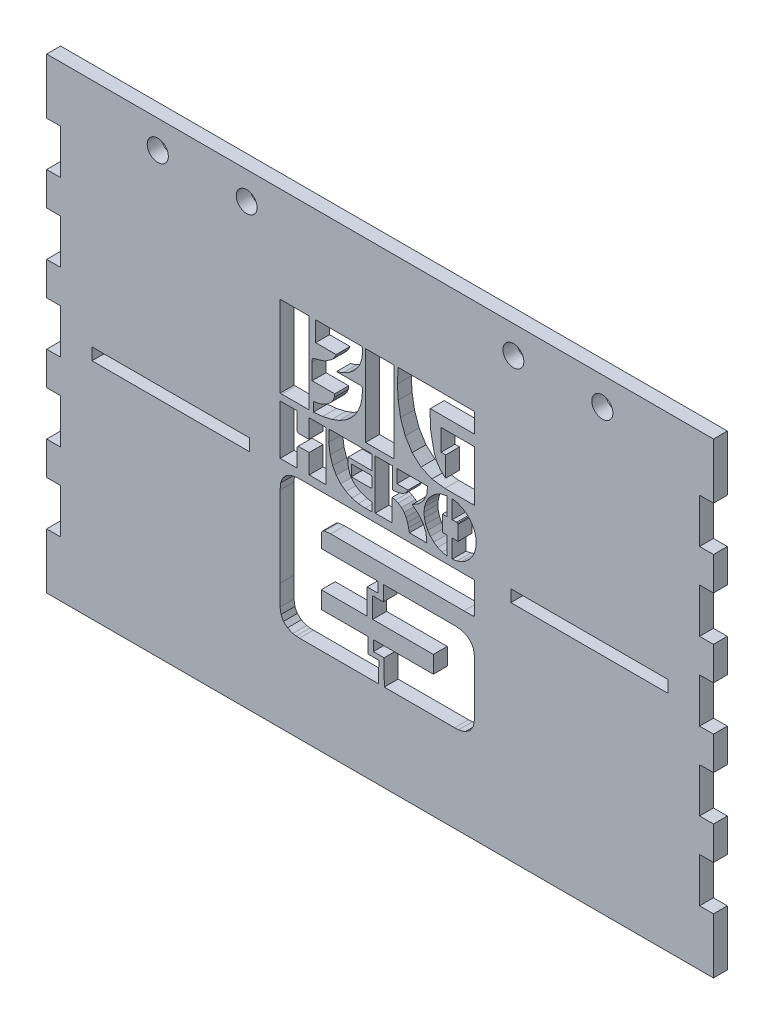
SolidWorks part; units mm, degrees
ref_plane "Front Plane" through (0, 0, 0) normal (0, 0, 1) x (1, 0, 0)
ref_plane "Top Plane" through (0, 0, 0) normal (0, 1, 0) x (1, 0, 0)
ref_plane "Right Plane" through (0, 0, 0) normal (1, 0, 0) x (0, 0, -1)
sketch "Sketch1" plane through (0, 0, 0) normal (0, 0, 1) x (1, 0, 0)
  line L0 (-83.4402, 53.069) -> (-83.4402, 40.369) construction
  line L1 (-83.4402, 53.069) -> (68.9598, 53.069)
  line L2 (-83.4402, 53.069) -> (-83.4402, -53.611)
  line L3 (-83.4402, -53.611) -> (68.9598, -53.611)
  line L4 (68.9598, 53.069) -> (68.9598, -53.611)
  line L5 (-83.4402, 46.719) -> (-58.0402, 46.719) construction
  line L6 (-7.2402, 53.069) -> (-7.2402, -53.611) construction
  line L7 (-47.8802, 46.719) -> (-37.7202, 46.719) construction
  line L8 (-55.6272, 46.719) -> (-47.8802, 46.719) construction
  line L9 (41.1468, 46.719) -> (33.3998, 46.719) construction
  line L10 (33.3998, 46.719) -> (23.2398, 46.719) construction
  line L11 (68.9598, 46.719) -> (43.5598, 46.719) construction
  line L12 (68.9598, -0.271) -> (-83.4402, -0.271) construction
  circle A0 centre (-58.0402, 46.719) radius 2.413
  circle A2 centre (-37.7202, 46.719) radius 2.3847
  circle A3 centre (23.2398, 46.719) radius 2.3847
  circle A5 centre (43.5598, 46.719) radius 2.413
  dimension "D4" = 4.826
  dimension "D7" = 10.16
  dimension "D8" = 4.7693
  dimension "D1" = 106.68
  dimension "D2" = 152.4
  dimension "D3" = 12.7
  dimension "D5" = 25.4
  dimension "D6" = 7.747
extrude "Boss-Extrude1" add sketch "Sketch1" along normal blind 3.175
sketch "Sketch2" plane through (0, 0, 3.175) normal (0, 0, 1) x (1, 0, 0)
  line L0 (-83.4402, 53.069) -> (-83.4402, -53.611) construction
  line L1 (-83.4402, 40.369) -> (-80.2652, 40.369)
  line L2 (-83.4402, 40.369) -> (-83.4402, 30.209)
  line L3 (-83.4402, 30.209) -> (-80.2652, 30.209)
  line L4 (-80.2652, 40.369) -> (-80.2652, 30.209)
  line L5 (-83.4402, 40.369) -> (-83.4402, 53.069) construction
  line L6 (-83.4402, 30.209) -> (-83.4402, -53.611) construction
  dimension "D1" = 3.175
  dimension "D2" = 12.7
  dimension "D3" = 10.16
extrude "Cut-Extrude1" cut sketch "Sketch2" against normal through all contours L4 L3 L2 L1
pattern_linear "LPattern1" count 5 spacing 17.78 along (0, -1, 0) of "Cut-Extrude1"
ref_plane "Plane1" through (-7.2402, 0, 0) normal (-1, 0, 0) x (0, 0, 1)
mirror "Mirror1" about plane through (-7.2402, 0, 0) normal (-1, 0, 0) of "LPattern1", "Cut-Extrude1"
sketch "Sketch3" plane through (0, 0.4582, 0) normal (0, 0, -1) x (-1, 0, 0)
  line L0 (22.4861, 14.3643) -> (22.4861, 12.2032)
  line L54 (7.2402, 52.6108) -> (7.2402, -54.0692) construction
  line L99 (-58.5963, -0.1731) -> (-22.6521, -0.1731)
  line L256 (-58.5963, -0.1731) -> (-58.5963, -2.9203)
  line L275 (-58.5963, -2.9203) -> (-22.6521, -2.9203)
  line L276 (-22.6521, -0.1731) -> (-22.6521, -2.9203)
  line L278 (-68.9598, 52.6108) -> (83.4402, 52.6108) construction
  line L280 (83.4402, -54.0692) -> (-68.9598, -54.0692) construction
  line L281 (37.1325, -0.1731) -> (37.1325, -2.9203)
  line L282 (73.0766, -2.9203) -> (37.1325, -2.9203)
  line L283 (73.0766, -0.1731) -> (73.0766, -2.9203)
  line L284 (73.0766, -0.1731) -> (37.1325, -0.1731)
  line L285 (21.9553, 26.2147) -> (21.9559, 30.7644)
  line L286 (10.1811, -16.2374) -> (10.2041, -22.0279)
  line L287 (7.7211, -16.2367) -> (10.1811, -16.2374)
  line L288 (7.7081, -13.8815) -> (7.7211, -16.2367)
  line L289 (8.9509, -17.3486) -> (8.918, -22.0279)
  line L290 (6.4902, -17.3486) -> (8.9509, -17.3486)
  line L291 (6.5045, -13.8809) -> (6.4902, -17.3486)
  line L292 (6.2986, -28.3222) -> (6.2763, -34.1128)
  line L293 (8.7592, -28.3222) -> (6.2986, -28.3222)
  line L294 (8.7592, -25.9557) -> (8.7592, -28.3222)
  line L295 (7.5289, -29.4334) -> (7.5624, -34.1128)
  line L296 (9.9895, -29.4334) -> (7.5289, -29.4334)
  line L297 (9.9945, -25.9557) -> (9.9895, -29.4334)
  line L298 (3.3859, 7.5801) -> (3.3989, 10.6193)
  line L299 (4.4518, 7.5801) -> (4.4476, 10.6193)
  line L300 (-9.2452, -1.0277) -> (-9.2452, 3.1617)
  line L301 (-8.054, -1.0016) -> (-8.0547, 3.1617)
  line L302 (-9.2452, 6.7777) -> (-9.2452, 10.9337)
  line L303 (-8.0547, 6.7759) -> (-8.0547, 10.9145)
  line L304 (13.8169, 3.7404) -> (13.8169, 6.3195)
  line L305 (9.3025, 3.7521) -> (13.8169, 3.7404)
  line L306 (9.1437, 3.852) -> (9.3025, 3.7521)
  line L307 (9.0494, 4.0225) -> (9.1437, 3.852)
  line L308 (9.0501, 6.0188) -> (9.0494, 4.0225)
  line L309 (9.1535, 6.201) -> (9.0501, 6.0188)
  line L310 (9.3266, 6.3065) -> (9.1535, 6.201)
  line L311 (13.8169, 6.3195) -> (9.3266, 6.3065)
  line L312 (9.0686, 7.3141) -> (14.5095, 7.3141)
  line L313 (9.0686, 10.6132) -> (9.0686, 7.3141)
  line L314 (9.267, 10.6558) -> (9.0686, 10.6132)
  line L315 (18.5775, 10.6634) -> (9.267, 10.6558)
  line L316 (18.8422, 10.5784) -> (18.5775, 10.6634)
  line L317 (18.9278, 10.3129) -> (18.8422, 10.5784)
  line L318 (18.9681, 7.9775) -> (18.9278, 10.3129)
  line L319 (18.6464, 5.6652) -> (18.9681, 7.9775)
  line L320 (18.0709, 3.8334) -> (18.6464, 5.6652)
  line L321 (17.2524, 2.3327) -> (18.0709, 3.8334)
  line L322 (16.2235, 1.1451) -> (17.2524, 2.3327)
  line L323 (15.0179, 0.2498) -> (16.2235, 1.1451)
  line L324 (13.6675, -0.3722) -> (15.0179, 0.2498)
  line L325 (12.2058, -0.74) -> (13.6675, -0.3722)
  line L326 (10.6642, -0.8739) -> (12.2058, -0.74)
  line L327 (9.0761, -0.7927) -> (10.6642, -0.8739)
  line L328 (9.0761, 1.0696) -> (9.0761, -0.7927)
  line L329 (10.4733, 1.3585) -> (9.0761, 1.0696)
  line L330 (11.6743, 1.7982) -> (10.4733, 1.3585)
  line L331 (12.6759, 2.3829) -> (11.6743, 1.7982)
  line L332 (13.472, 3.1079) -> (12.6759, 2.3829)
  line L333 (14.0586, 3.9685) -> (13.472, 3.1079)
  line L334 (14.4301, 4.9596) -> (14.0586, 3.9685)
  line L335 (14.582, 6.0771) -> (14.4301, 4.9596)
  line L336 (14.5095, 7.3141) -> (14.582, 6.0771)
  line L337 (26.2049, -0.1731) -> (26.2049, -0.7245)
  line L338 (26.195, 3.3237) -> (26.2049, -0.1731)
  line L339 (26.1163, 3.5692) -> (26.195, 3.3237)
  line L340 (25.9798, 3.7144) -> (26.1163, 3.5692)
  line L341 (23.4466, 3.7316) -> (25.9798, 3.7144)
  line L342 (23.4466, -0.7108) -> (23.4466, 3.7316)
  line L343 (19.5902, -0.7108) -> (23.4466, -0.7108)
  line L344 (19.5902, 10.628) -> (19.5902, -0.7108)
  line L345 (23.472, 10.628) -> (19.5902, 10.628)
  line L346 (23.472, 6.322) -> (23.472, 10.628)
  line L347 (25.7572, 6.3145) -> (23.472, 6.322)
  line L348 (25.9867, 6.3356) -> (25.7572, 6.3145)
  line L349 (26.1262, 6.42) -> (25.9867, 6.3356)
  line L350 (26.195, 6.5706) -> (26.1262, 6.42)
  line L351 (26.2111, 6.7908) -> (26.195, 6.5706)
  line L352 (26.2062, 10.1066) -> (26.2111, 6.7908)
  line L353 (26.2409, 10.6329) -> (26.2062, 10.1066)
  line L354 (30.0627, 10.6329) -> (26.2409, 10.6329)
  line L355 (30.0627, -0.7245) -> (30.0627, 10.6329)
  line L356 (26.2049, -0.7245) -> (30.0627, -0.7245)
  line L357 (-6.9992, 10.6883) -> (-8.0547, 10.9145)
  line L358 (-6.0194, 10.2788) -> (-6.9992, 10.6883)
  line L359 (-5.1333, 9.7053) -> (-6.0194, 10.2788)
  line L360 (-4.3613, 8.9878) -> (-5.1333, 9.7053)
  line L361 (-3.7225, 8.1444) -> (-4.3613, 8.9878)
  line L362 (-3.237, 7.1951) -> (-3.7225, 8.1444)
  line L363 (-2.9232, 6.1588) -> (-3.237, 7.1951)
  line L364 (-2.8022, 5.0543) -> (-2.9232, 6.1588)
  line L365 (-2.8904, 3.9184) -> (-2.8022, 5.0543)
  line L366 (-3.1792, 2.8506) -> (-2.8904, 3.9184)
  line L367 (-3.6506, 1.8708) -> (-3.1792, 2.8506)
  line L368 (-4.2842, 0.9994) -> (-3.6506, 1.8708)
  line L369 (-5.0608, 0.2566) -> (-4.2842, 0.9994)
  line L370 (-5.9611, -0.338) -> (-5.0608, 0.2566)
  line L371 (-6.9652, -0.7641) -> (-5.9611, -0.338)
  line L372 (-8.054, -1.0016) -> (-6.9652, -0.7641)
  line L373 (-10.3564, -0.8355) -> (-9.2452, -1.0277)
  line L374 (-11.3859, -0.4492) -> (-10.3564, -0.8355)
  line L375 (-12.3137, 0.1127) -> (-11.3859, -0.4492)
  line L376 (-13.1204, 0.8308) -> (-12.3137, 0.1127)
  line L377 (-13.7858, 1.6847) -> (-13.1204, 0.8308)
  line L378 (-14.29, 2.6558) -> (-13.7858, 1.6847)
  line L379 (-14.6137, 3.7249) -> (-14.29, 2.6558)
  line L380 (-14.7364, 4.8714) -> (-14.6137, 3.7249)
  line L381 (-14.6417, 6.0404) -> (-14.7364, 4.8714)
  line L382 (-14.3377, 7.1324) -> (-14.6417, 6.0404)
  line L383 (-13.8448, 8.1277) -> (-14.3377, 7.1324)
  line L384 (-13.1831, 9.0058) -> (-13.8448, 8.1277)
  line L385 (-12.372, 9.7456) -> (-13.1831, 9.0058)
  line L386 (-11.4325, 10.3279) -> (-12.372, 9.7456)
  line L387 (-10.3832, 10.7303) -> (-11.4325, 10.3279)
  line L388 (-9.2452, 10.9337) -> (-10.3832, 10.7303)
  line L389 (-10.2368, 6.7647) -> (-9.2452, 6.7777)
  line L390 (-10.4452, 6.6802) -> (-10.2368, 6.7647)
  line L391 (-10.5669, 6.5364) -> (-10.4452, 6.6802)
  line L392 (-10.5822, 3.1617) -> (-10.5669, 6.5364)
  line L393 (-9.2452, 3.1617) -> (-10.5822, 3.1617)
  line L394 (-6.9999, 3.1617) -> (-8.0547, 3.1617)
  line L395 (-6.9999, 6.7759) -> (-6.9999, 3.1617)
  line L396 (-7.8822, 6.7759) -> (-6.9999, 6.7759)
  line L397 (-8.0547, 6.7759) -> (-7.8822, 6.7759)
  line L398 (8.3443, 10.6193) -> (4.4476, 10.6193)
  line L399 (8.3443, -0.7134) -> (8.3443, 10.6193)
  line L400 (4.4655, -0.7134) -> (8.3443, -0.7134)
  line L401 (4.4655, 4.3581) -> (4.4655, -0.7134)
  line L402 (3.748, 4.1467) -> (4.4655, 4.3581)
  line L403 (3.1123, 3.9147) -> (3.748, 4.1467)
  line L404 (2.331, 3.4104) -> (3.1123, 3.9147)
  line L405 (1.7301, 2.7593) -> (2.331, 3.4104)
  line L406 (1.2806, 1.9905) -> (1.7301, 2.7593)
  line L407 (0.9532, 1.1315) -> (1.2806, 1.9905)
  line L408 (0.7262, 0.2151) -> (0.9532, 1.1315)
  line L409 (0.5333, -0.717) -> (0.7262, 0.2151)
  line L410 (-3.4404, -0.717) -> (0.5333, -0.717)
  line L411 (-3.2643, 1.1434) -> (-3.4404, -0.717)
  line L412 (-2.6069, 2.7258) -> (-3.2643, 1.1434)
  line L413 (-1.5304, 4.0716) -> (-2.6069, 2.7258)
  line L414 (-0.0998, 5.2199) -> (-1.5304, 4.0716)
  line L415 (-1.6433, 6.1446) -> (-0.0998, 5.2199)
  line L416 (-2.7644, 7.3817) -> (-1.6433, 6.1446)
  line L417 (-3.4348, 8.8874) -> (-2.7644, 7.3817)
  line L418 (-3.6284, 10.6193) -> (-3.4348, 8.8874)
  line L419 (3.3989, 10.6193) -> (-3.6284, 10.6193)
  line L420 (0.8836, 7.5801) -> (3.3859, 7.5801)
  line L421 (1.2508, 6.8454) -> (0.8836, 7.5801)
  line L422 (2.0929, 6.2934) -> (1.2508, 6.8454)
  line L423 (3.2229, 5.9529) -> (2.0929, 6.2934)
  line L424 (4.4518, 5.8513) -> (3.2229, 5.9529)
  line L425 (4.4518, 7.5801) -> (4.4518, 5.8513)
  line L426 (10.5433, 12.1783) -> (10.5433, 30.7533)
  line L427 (4.037, 12.1783) -> (10.5433, 12.1783)
  line L428 (4.037, 30.7533) -> (4.037, 12.1783)
  line L429 (10.5433, 30.7533) -> (4.037, 30.7533)
  line L430 (-6.7077, 23.7794) -> (-14.3197, 23.7794)
  line L431 (-6.7077, 18.8638) -> (-6.7077, 23.7794)
  line L432 (-7.7595, 18.8638) -> (-6.7077, 18.8638)
  line L433 (-7.7595, 14.2544) -> (-7.7595, 18.8638)
  line L434 (-7.1368, 14.7456) -> (-7.7595, 14.2544)
  line L435 (-6.6167, 15.2088) -> (-7.1368, 14.7456)
  line L436 (-5.6952, 16.5539) -> (-6.6167, 15.2088)
  line L437 (-5.1054, 18.0738) -> (-5.6952, 16.5539)
  line L438 (-4.3259, 22.0295) -> (-5.1054, 18.0738)
  line L439 (-4.1658, 26.059) -> (-4.3259, 22.0295)
  line L440 (-4.2377, 26.2674) -> (-4.1658, 26.059)
  line L441 (-14.3128, 26.2674) -> (-4.2377, 26.2674)
  line L442 (-14.3128, 30.7595) -> (-14.3128, 26.2674)
  line L443 (3.0826, 30.7595) -> (-14.3128, 30.7595)
  line L444 (3.123, 30.504) -> (3.0826, 30.7595)
  line L445 (3.2736, 27.3762) -> (3.123, 30.504)
  line L446 (3.0938, 24.2513) -> (3.2736, 27.3762)
  line L447 (2.5518, 21.0603) -> (3.0938, 24.2513)
  line L448 (1.4884, 18.0012) -> (2.5518, 21.0603)
  line L449 (-0.0856, 15.4661) -> (1.4884, 18.0012)
  line L450 (-2.117, 13.6388) -> (-0.0856, 15.4661)
  line L451 (-4.6131, 12.5318) -> (-2.117, 13.6388)
  line L452 (-7.5803, 12.156) -> (-4.6131, 12.5318)
  line L453 (-13.8008, 12.1517) -> (-7.5803, 12.156)
  line L454 (-14.3197, 12.1517) -> (-13.8008, 12.1517)
  line L455 (-14.3197, 23.7794) -> (-14.3197, 12.1517)
  line L456 (30.0546, 30.7644) -> (23.4981, 30.7644)
  line L457 (30.0546, 12.1857) -> (30.0546, 30.7644)
  line L458 (29.6968, 12.1665) -> (30.0546, 12.1857)
  line L459 (23.4981, 12.1727) -> (29.6968, 12.1665)
  line L460 (20.3448, 12.4252) -> (22.4861, 12.2032)
  line L461 (18.2378, 12.8988) -> (20.3448, 12.4252)
  line L462 (16.6235, 13.5017) -> (18.2378, 12.8988)
  line L463 (15.204, 14.2936) -> (16.6235, 13.5017)
  line L464 (13.9887, 15.2635) -> (15.204, 14.2936)
  line L465 (12.9853, 16.3988) -> (13.9887, 15.2635)
  line L466 (12.2033, 17.688) -> (12.9853, 16.3988)
  line L467 (11.6507, 19.1187) -> (12.2033, 17.688)
  line L468 (11.337, 20.6789) -> (11.6507, 19.1187)
  line L469 (11.2694, 22.3568) -> (11.337, 20.6789)
  line L470 (11.3023, 22.6124) -> (11.2694, 22.3568)
  line L471 (11.3922, 22.78) -> (11.3023, 22.6124)
  line L472 (11.559, 22.8716) -> (11.3922, 22.78)
  line L473 (11.822, 22.8959) -> (11.559, 22.8716)
  line L474 (16.7251, 22.8865) -> (11.822, 22.8959)
  line L475 (17.1867, 22.8865) -> (16.7251, 22.8865)
  line L476 (15.756, 23.3678) -> (17.1867, 22.8865)
  line L477 (14.4952, 24.0295) -> (15.756, 23.3678)
  line L478 (13.4188, 24.8535) -> (14.4952, 24.0295)
  line L479 (12.542, 25.8216) -> (13.4188, 24.8535)
  line L480 (11.8783, 26.9153) -> (12.542, 25.8216)
  line L481 (11.4437, 28.1159) -> (11.8783, 26.9153)
  line L482 (11.2527, 29.4052) -> (11.4437, 28.1159)
  line L483 (11.3198, 30.7644) -> (11.2527, 29.4052)
  line L484 (21.9559, 30.7644) -> (11.3198, 30.7644)
  line L485 (17.2771, 26.2147) -> (21.9553, 26.2147)
  line L486 (17.6431, 25.4253) -> (17.2771, 26.2147)
  line L487 (18.1861, 24.768) -> (17.6431, 25.4253)
  line L488 (19.9343, 23.6027) -> (18.1861, 24.768)
  line L489 (21.946, 22.9976) -> (19.9343, 23.6027)
  line L490 (22.4173, 22.8928) -> (21.946, 22.9976)
  line L491 (22.6604, 22.7569) -> (22.4173, 22.8928)
  line L492 (22.7502, 22.4927) -> (22.6604, 22.7569)
  line L493 (22.7632, 22.0016) -> (22.7502, 22.4927)
  line L494 (22.7632, 18.2822) -> (22.7632, 22.0016)
  line L495 (17.5933, 18.2822) -> (22.7632, 18.2822)
  line L496 (17.6665, 17.548) -> (17.5933, 18.2822)
  line L497 (17.9518, 16.8484) -> (17.6665, 17.548)
  line L498 (18.4206, 16.2016) -> (17.9518, 16.8484)
  line L499 (19.0432, 15.6249) -> (18.4206, 16.2016)
  line L500 (19.7904, 15.1356) -> (19.0432, 15.6249)
  line L501 (20.6332, 14.7505) -> (19.7904, 15.1356)
  line L502 (21.5416, 14.4883) -> (20.6332, 14.7505)
  line L503 (22.4861, 14.3643) -> (21.5416, 14.4883)
  line L504 (20.1302, -13.8845) -> (7.7081, -13.8815)
  line L505 (20.6326, -13.8845) -> (20.1302, -13.8845)
  line L506 (20.6276, -10.8702) -> (20.6326, -13.8845)
  line L507 (20.5687, -10.549) -> (20.6276, -10.8702)
  line L508 (20.413, -10.3009) -> (20.5687, -10.549)
  line L509 (20.1768, -10.1272) -> (20.413, -10.3009)
  line L510 (19.8742, -10.0293) -> (20.1768, -10.1272)
  line L511 (18.5229, -9.9114) -> (19.8742, -10.0293)
  line L512 (-11.9558, -9.9072) -> (18.5229, -9.9114)
  line L513 (-13.9091, -9.914) -> (-11.9558, -9.9072)
  line L514 (-14.1206, -9.8984) -> (-13.9091, -9.914)
  line L515 (-14.2572, -9.8285) -> (-14.1206, -9.8984)
  line L516 (-14.329, -9.6913) -> (-14.2572, -9.8285)
  line L517 (-14.3482, -9.4781) -> (-14.329, -9.6913)
  line L518 (-14.3414, -6.0264) -> (-14.3482, -9.4781)
  line L519 (-14.3414, -2.5823) -> (-14.3414, -6.0264)
  line L520 (-13.6574, -2.5823) -> (-14.3414, -2.5823)
  line L521 (25.5879, -2.5836) -> (-13.6574, -2.5823)
  line L522 (26.4945, -2.6288) -> (25.5879, -2.5836)
  line L523 (27.7484, -2.9203) -> (26.4945, -2.6288)
  line L524 (28.7722, -3.5205) -> (27.7484, -2.9203)
  line L525 (29.5232, -4.3992) -> (28.7722, -3.5205)
  line L526 (29.9585, -5.5254) -> (29.5232, -4.3992)
  line L527 (30.0863, -7.0123) -> (29.9585, -5.5254)
  line L528 (30.0838, -25.4541) -> (30.0863, -7.0123)
  line L529 (30.0832, -30.1782) -> (30.0838, -25.4541)
  line L530 (29.8767, -31.5418) -> (30.0832, -30.1782)
  line L531 (29.313, -32.6363) -> (29.8767, -31.5418)
  line L532 (28.407, -33.4425) -> (29.313, -32.6363)
  line L533 (27.1729, -33.941) -> (28.407, -33.4425)
  line L534 (26.4158, -34.0682) -> (27.1729, -33.941)
  line L535 (25.6456, -34.1066) -> (26.4158, -34.0682)
  line L536 (7.5624, -34.1128) -> (25.6456, -34.1066)
  line L537 (23.4981, 30.7644) -> (23.4981, 12.1727)
  line L538 (-9.8301, -34.1116) -> (6.2763, -34.1128)
  line L539 (-10.6921, -34.0806) -> (-9.8301, -34.1116)
  line L540 (-12.1691, -33.719) -> (-10.6921, -34.0806)
  line L541 (-13.3127, -32.9315) -> (-12.1691, -33.719)
  line L542 (-14.0548, -31.7712) -> (-13.3127, -32.9315)
  line L543 (-14.3271, -30.2948) -> (-14.0548, -31.7712)
  line L544 (-14.3265, -17.6674) -> (-14.3271, -30.2948)
  line L545 (-14.1188, -16.3545) -> (-14.3265, -17.6674)
  line L546 (-13.5396, -15.2998) -> (-14.1188, -16.3545)
  line L547 (-12.6169, -14.5196) -> (-13.5396, -15.2998)
  line L548 (-11.3772, -14.0353) -> (-12.6169, -14.5196)
  line L549 (-9.9852, -13.8834) -> (-11.3772, -14.0353)
  line L550 (6.5045, -13.8809) -> (-9.9852, -13.8834)
  line L551 (20.6617, -25.9557) -> (9.9945, -25.9557)
  line L552 (20.6617, -22.0279) -> (20.6617, -25.9557)
  line L553 (10.2041, -22.0279) -> (20.6617, -22.0279)
  line L554 (-4.9423, -22.0279) -> (8.918, -22.0279)
  line L555 (-4.9423, -25.9557) -> (-4.9423, -22.0279)
  line L556 (8.7592, -25.9557) -> (-4.9423, -25.9557)
extrude "Cut-Extrude2" cut sketch "Sketch3" against normal up to next
